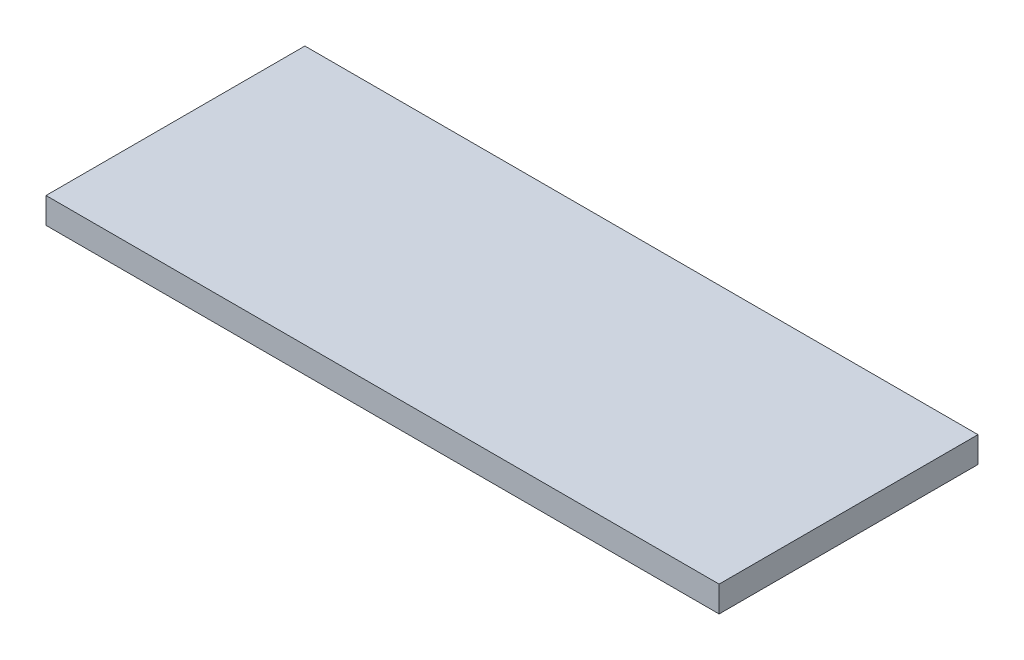
SolidWorks part; units mm, degrees
ref_plane "Front Plane" through (0, 0, 0) normal (0, 0, 1) x (1, 0, 0)
ref_plane "Top Plane" through (0, 0, 0) normal (0, 1, 0) x (1, 0, 0)
ref_plane "Right Plane" through (0, 0, 0) normal (1, 0, 0) x (0, 0, -1)
sketch "Sketch1" plane through (0, 0, 0) normal (0, 1, 0) x (1, 0, 0)
  line L0 (-130, 50) -> (130, -50) construction
  line L1 (-130, 50) -> (130, 50)
  line L2 (-130, 50) -> (-130, -50)
  line L3 (-130, -50) -> (130, -50)
  line L4 (130, 50) -> (130, -50)
  dimension "D1" = 260
  dimension "D2" = 100
extrude "Boss-Extrude1" add sketch "Sketch1" along normal blind 10
